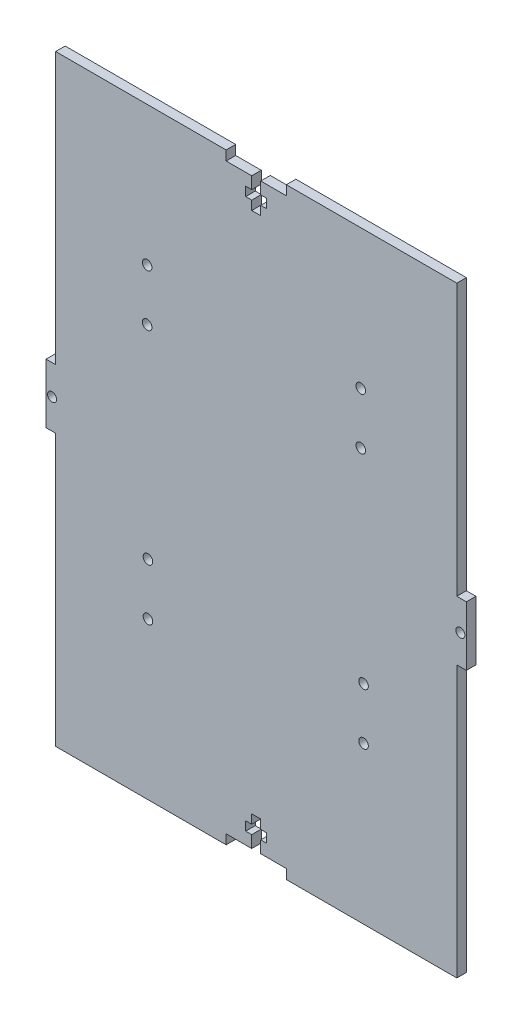
SolidWorks part; units mm, degrees
ref_plane "Front Plane" through (0, 0, 0) normal (0, 0, 1) x (1, 0, 0)
ref_plane "Top Plane" through (0, 0, 0) normal (0, 1, 0) x (1, 0, 0)
ref_plane "Right Plane" through (0, 0, 0) normal (1, 0, 0) x (0, 0, -1)
sketch "Sketch1" plane through (0, 0, 0) normal (0, 0, 1) x (1, 0, 0)
  line L1 (-69.85, 100.01) -> (69.85, 100.01)
  line L2 (-69.85, 100.01) -> (-69.85, -100.01)
  line L3 (-69.85, -100.01) -> (69.85, -100.01)
  line L4 (69.85, 100.01) -> (69.85, -100.01)
  line L5 (-69.85, 100.01) -> (69.85, -100.01) construction
  line L6 (-69.85, -100.01) -> (69.85, 100.01) construction
  point P0 (0, 0)
  dimension "D1" = 200.02
  dimension "D2" = 139.7
extrude "Boss-Extrude1" add sketch "Sketch1" along normal blind 3.18
sketch "Sketch2" plane through (0, 0, 3.18) normal (0, 0, 1) x (1, 0, 0)
  line L0 (0, 0) -> (69.85, 0) construction
  line L1 (-10, 100.01) -> (10, 100.01)
  line L2 (-10, 100.01) -> (-10, 96.83)
  line L3 (-10, 96.83) -> (-1.5, 96.83)
  line L4 (10, 100.01) -> (10, 96.83)
  line L5 (69.85, -100.01) -> (69.85, 100.01) construction
  line L6 (0, 0) -> (0, 100.01) construction
  line L7 (-1.5, 86.83) -> (1.5, 86.83)
  line L8 (-1.5, 86.83) -> (-1.5, 89.83)
  line L10 (1.5, 86.83) -> (1.5, 89.83)
  line L12 (69.85, 100.01) -> (-69.85, 100.01) construction
  line L13 (3.5, 92.83) -> (1.5, 92.83)
  line L14 (3.5, 92.83) -> (3.5, 89.83)
  line L15 (3.5, 89.83) -> (1.5, 89.83)
  line L16 (-3.5, 92.83) -> (-3.5, 89.83)
  line L17 (-10, -100.01) -> (-10, -96.83)
  line L18 (-10, -96.83) -> (-1.5, -96.83)
  line L19 (-1.5, -92.83) -> (-1.5, -96.83)
  line L20 (-1.5, -92.83) -> (-3.5, -92.83)
  line L21 (-3.5, -92.83) -> (-3.5, -89.83)
  line L22 (1.5, 96.83) -> (10, 96.83)
  line L23 (-1.5, 92.83) -> (-3.5, 92.83)
  line L24 (-1.5, -89.83) -> (-3.5, -89.83)
  line L25 (-1.5, -86.83) -> (-1.5, -89.83)
  line L26 (-1.5, -86.83) -> (1.5, -86.83)
  line L27 (-1.5, 89.83) -> (-3.5, 89.83)
  line L28 (1.5, -86.83) -> (1.5, -89.83)
  line L29 (-1.5, 92.83) -> (-1.5, 96.83)
  line L30 (1.5, 92.83) -> (1.5, 96.83)
  line L31 (3.5, -89.83) -> (1.5, -89.83)
  line L32 (3.5, -92.83) -> (3.5, -89.83)
  line L33 (3.5, -92.83) -> (1.5, -92.83)
  line L34 (1.5, -92.83) -> (1.5, -96.83)
  line L35 (1.5, -96.83) -> (10, -96.83)
  line L36 (10, -100.01) -> (10, -96.83)
  line L37 (-10, -100.01) -> (10, -100.01)
  line L38 (-69.85, 100.01) -> (-69.85, -100.01) construction
  line L39 (-69.85, 100.01) -> (-66.67, 100.01)
  line L40 (-69.85, 100.01) -> (-69.85, 9.875)
  line L41 (-69.85, 9.875) -> (-66.67, 9.875)
  line L42 (-66.67, 100.01) -> (-66.67, 9.875)
  line L43 (-69.85, -100.01) -> (-66.67, -100.01)
  line L44 (-69.85, -100.01) -> (-69.85, -9.875)
  line L45 (-69.85, -9.875) -> (-66.67, -9.875)
  line L46 (-66.67, -100.01) -> (-66.67, -9.875)
  line L47 (69.85, -9.875) -> (66.67, -9.875)
  line L48 (66.67, -100.01) -> (66.67, -9.875)
  line L49 (69.85, -100.01) -> (66.67, -100.01)
  line L50 (69.85, -100.01) -> (69.85, -9.875)
  line L51 (69.85, 9.875) -> (66.67, 9.875)
  line L52 (66.67, 100.01) -> (66.67, 9.875)
  line L53 (69.85, 100.01) -> (66.67, 100.01)
  line L54 (69.85, 100.01) -> (69.85, 9.875)
  circle A0 centre (-67.85, 0) radius 1.5
  circle A1 centre (67.85, 0) radius 1.5
  point P0 (0, 50.5662)
  point P5 (0, 32.0079)
  point P10 (15.4931, 34.4893)
  dimension "D11" = 3
  dimension "D12" = 2
  dimension "D1" = 20
  dimension "D2" = 19.75
  dimension "D3" = 4
  dimension "D4" = 3
  dimension "D5" = 3.18
  dimension "D6" = 7
  dimension "D7" = 3
  dimension "D8" = 3
  dimension "D9" = 3.18
  dimension "D10" = 3.18
extrude "Cut-Extrude1" cut sketch "Sketch2" against normal through all
sketch "Sketch3" plane through (0, 0, 0) normal (0, 0, -1) x (-1, 0, 0)
  circle A0 centre (-35.6713, -47.9634) radius 1.59
  circle A1 centre (-35.6713, -30.7773) radius 1.59
extrude "Cut-Extrude2" cut sketch "Sketch3" against normal through all
sketch "Sketch4" plane through (0, 0, 0) normal (0, 0, -1) x (-1, 0, 0)
  circle A0 centre (-34.7507, 53.7803) radius 1.59
  circle A1 centre (-34.7507, 36.5942) radius 1.59
  circle A2 centre (36.2498, 53.7803) radius 1.59
  circle A3 centre (36.2498, 36.5942) radius 1.59
  circle A4 centre (35.9839, -30.7773) radius 1.59
  circle A5 centre (35.9839, -47.9634) radius 1.59
  circle A6 centre (-35.6713, -30.7773) radius 1.59
  circle A7 centre (-35.6713, -47.9634) radius 1.59
extrude "Cut-Extrude3" cut sketch "Sketch4" against normal through all
